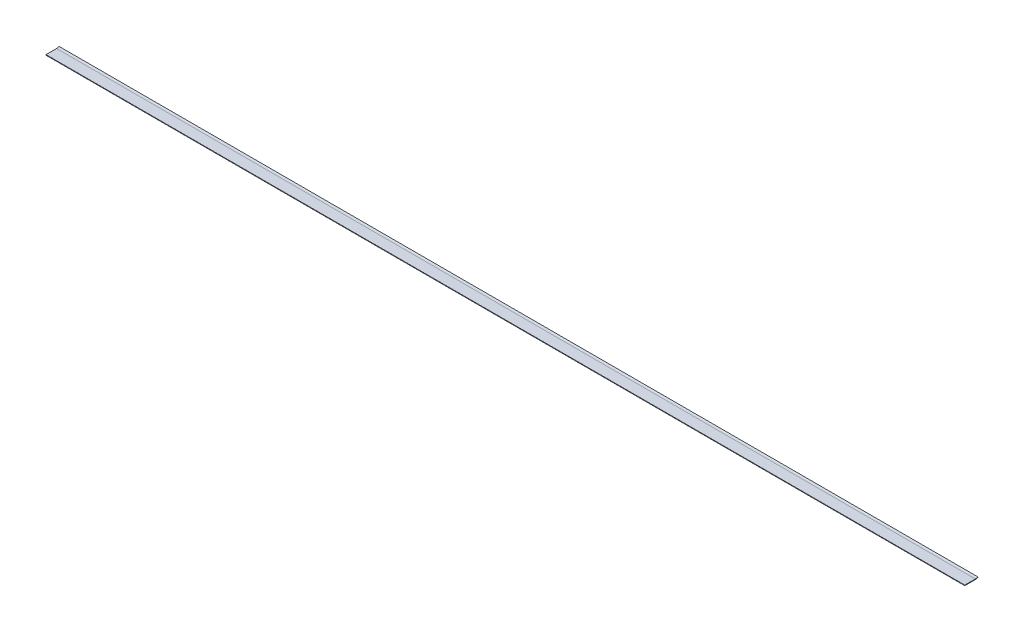
SolidWorks part; units mm, degrees
material "PVC 0.007 Plasticized"
ref_plane "Front Plane" through (0, 0, 0) normal (0, 0, 1) x (1, 0, 0)
ref_plane "Top Plane" through (0, 0, 0) normal (0, 1, 0) x (1, 0, 0)
ref_plane "Right Plane" through (0, 0, 0) normal (1, 0, 0) x (0, 0, -1)
sketch "Sketch1" plane through (0, 0, 0) normal (1, 0, 0) x (0, 0, -1)
  line L0 (0, 0) -> (-2.5146, 0)
  line L1 (1.7399, 0) -> (-1.7399, 0) construction
  arc A1 (0, 0) -> (0.6149, 0.2072) centre (0, 1.016) ccw
  dimension "D2" = 1.016
  dimension "D5" = 0.6604
  dimension "D1" = 2.5146
extrude "Extrude-Thin1" add sketch "Sketch1" against normal blind 217.4875 thin contours L0
